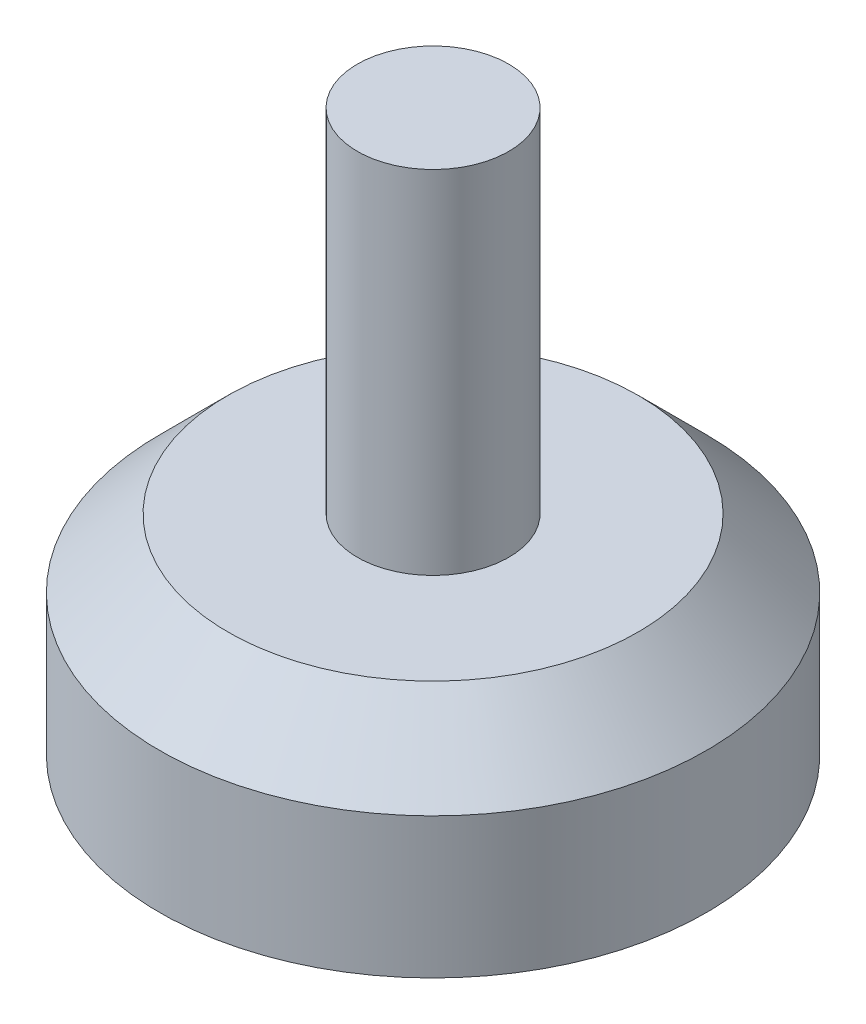
SolidWorks part; units mm, degrees
ref_plane "Front Plane" through (0, 0, 0) normal (0, 0, 1) x (1, 0, 0)
ref_plane "Top Plane" through (0, 0, 0) normal (0, 1, 0) x (1, 0, 0)
ref_plane "Right Plane" through (0, 0, 0) normal (1, 0, 0) x (0, 0, -1)
sketch "Sketch6" plane through (0, 0, 0) normal (0, 0, 1) x (1, 0, 0)
  line L0 (0, 0) -> (0, 90.2698) construction
  line L1 (0, 90.2698) -> (0, 0)
  line L2 (0, 0) -> (-44.0532, 0)
  line L3 (-44.0532, 0) -> (-44.0532, 22.6166)
  line L4 (-44.0532, 22.6166) -> (-33.0399, 33.6299)
  line L5 (-33.0399, 33.6299) -> (-12.1933, 33.6299)
  line L6 (-12.1933, 33.6299) -> (-12.1933, 90.2698)
  line L7 (-12.1933, 90.2698) -> (0, 90.2698)
revolve "Revolve2" add sketch "Sketch6" angle 360 about L0
